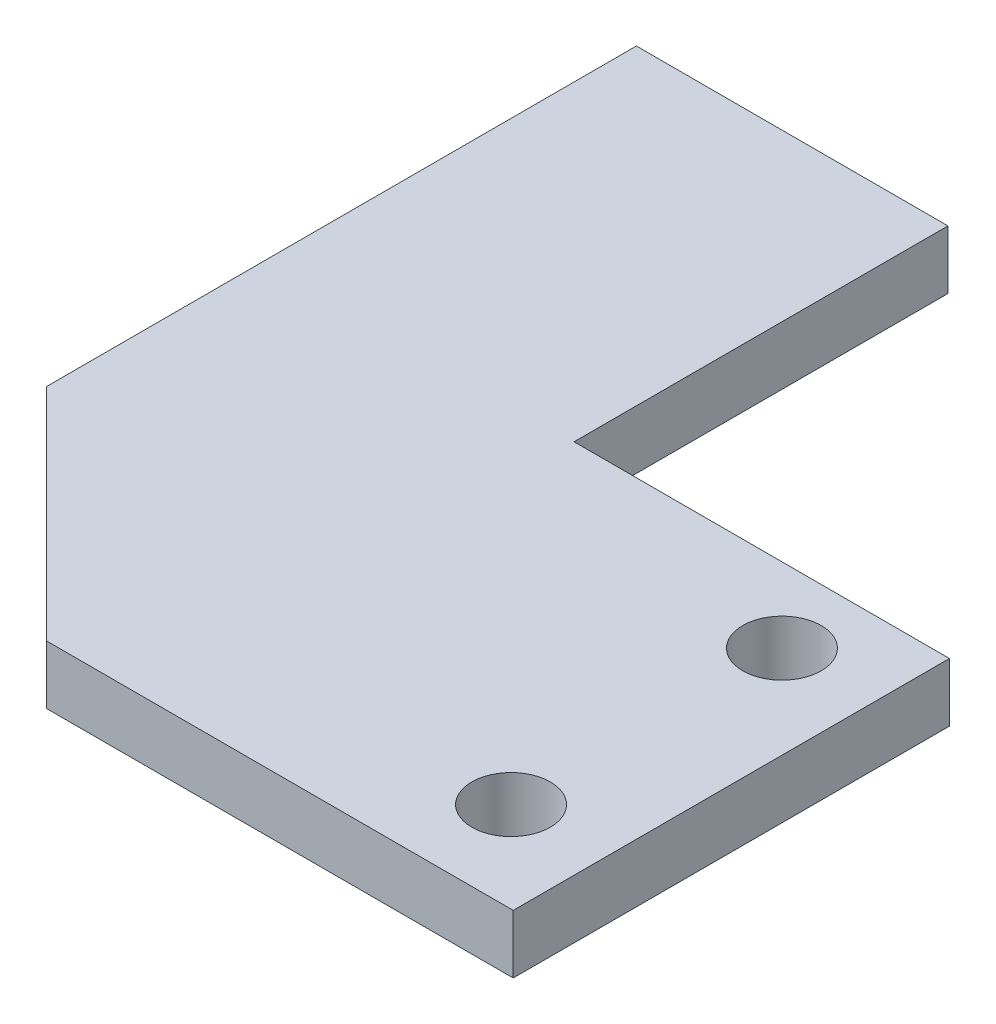
SolidWorks part; units mm, degrees
ref_plane "Front Plane" through (0, 0, 0) normal (0, 0, 1) x (1, 0, 0)
ref_plane "Top Plane" through (0, 0, 0) normal (0, 1, 0) x (1, 0, 0)
ref_plane "Right Plane" through (0, 0, 0) normal (1, 0, 0) x (0, 0, -1)
sketch "Sketch1" plane through (0, 0, 0) normal (0, 1, 0) x (1, 0, 0)
  line L0 (0, 36.83) -> (60.5539, 36.83) construction
  line L1 (0, 0) -> (70, 0)
  line L2 (0, 0) -> (0, 44.45)
  line L3 (0, 44.45) -> (70, 44.45)
  line L4 (70, 0) -> (70, 44.45)
  line L5 (0, 9.2261) -> (60.5539, 9.2261) construction
  circle A0 centre (60.5539, 36.83) radius 4
  circle A1 centre (60.5539, 9.2261) radius 4
  dimension "D4" = 8
  dimension "D1" = 70
  dimension "D2" = 44.45
  dimension "D3" = 60.5539
  dimension "D5" = 27.6039
  dimension "D6" = 7.62
extrude "Boss-Extrude1" add sketch "Sketch1" along normal blind 5.969
sketch "Sketch2" plane through (0, 5.969, 0) normal (0, 1, 0) x (1, 0, 0)
  line L0 (70, 44.45) -> (0, 44.45) construction
  line L1 (0, 44.45) -> (31.75, 44.45)
  line L2 (0, 44.45) -> (0, 82.55)
  line L3 (0, 82.55) -> (31.75, 82.55)
  line L4 (31.75, 44.45) -> (31.75, 82.55)
  line L5 (0, 44.45) -> (31.75, 82.55) construction
  line L6 (0, 82.55) -> (31.75, 44.45) construction
  point P4 (15.875, 63.5)
  dimension "D1" = 31.75
  dimension "D2" = 38.1
extrude "Boss-Extrude3" add sketch "Sketch2" against normal blind 5.969
sketch "Sketch3" plane through (0, 5.969, 0) normal (0, 1, 0) x (1, 0, 0)
  line L0 (0, 22.4506) -> (22.4506, 0)
  line L1 (0, 82.55) -> (0, 0) construction
  line L2 (0, 0) -> (70, 0) construction
  line L3 (22.4506, 0) -> (0, 0)
  line L4 (0, 0) -> (0, 22.4506)
  dimension "D1" = 45
  dimension "D2" = 31.75
extrude "Cut-Extrude1" cut sketch "Sketch3" against normal through all
